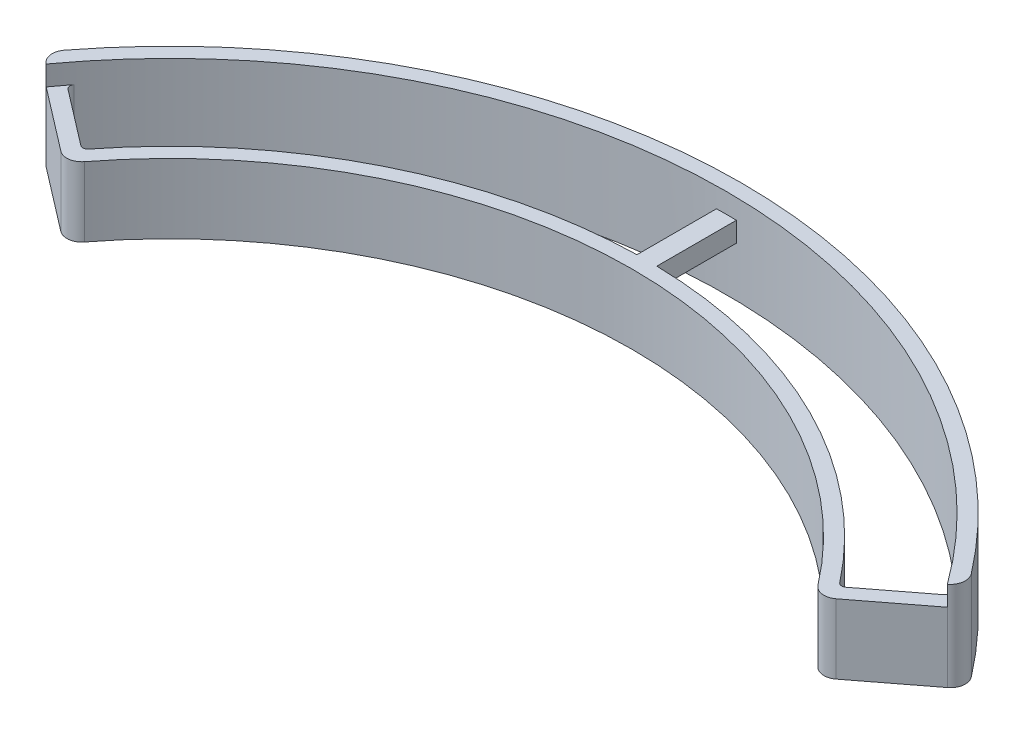
SolidWorks part; units mm, degrees
ref_plane "Front Plane" through (0, 0, 0) normal (0, 0, 1) x (1, 0, 0)
ref_plane "Top Plane" through (0, 0, 0) normal (0, 1, 0) x (1, 0, 0)
ref_plane "Right Plane" through (0, 0, 0) normal (1, 0, 0) x (0, 0, -1)
sketch "Sketch1" plane through (0, 0, 0) normal (0, 1, 0) x (1, 0, 0)
  line L0 (37.7849, 27.1026) -> (46.5154, 33.8018)
  line L1 (-37.7849, 27.1026) -> (-46.5154, 33.8018)
  line L2 (0, 48) -> (0, 56) construction
  line L3 (-38.081, 29.2205) -> (0, 0) construction
  line L4 (38.081, 29.2205) -> (0, 0) construction
  line L5 (-38.081, 29.2205) -> (-44.4278, 34.0906)
  line L6 (38.081, 29.2205) -> (44.4278, 34.0906)
  arc A0 (-44.4278, 34.0906) -> (44.4278, 34.0906) centre (0, 0) cw
  arc A1 (-38.081, 29.2205) -> (38.081, 29.2205) centre (0, 0) cw
  arc A2 (-37.7849, 27.1026) -> (37.7849, 27.1026) centre (0, 0) cw
  arc A3 (-46.5154, 33.8018) -> (46.5154, 33.8018) centre (0, 0) cw
  dimension "D1" = 56
  dimension "D2" = 105
  dimension "D3" = 8
  dimension "D4" = 1.5
extrude "Boss-Extrude1" add sketch "Sketch1" against normal blind 7
sketch "Sketch2" plane through (0, 0, 0) normal (0, 1, 0) x (1, 0, 0)
  line L1 (-1, 56.7595) -> (1, 56.7595)
  line L2 (-1, 56.7595) -> (-1, 47.003)
  line L3 (-1, 47.003) -> (1, 47.003)
  line L4 (1, 56.7595) -> (1, 47.003)
  line L5 (-1, 56.7595) -> (1, 47.003) construction
  line L6 (-1, 47.003) -> (1, 56.7595) construction
  point P0 (0, 51.8812)
  dimension "D1" = 2
extrude "Boss-Extrude2" add sketch "Sketch2" against normal blind 2
sketch "Sketch3" plane through (0, 0, 0) normal (0, 1, 0) x (1, 0, 0)
  line L0 (-46.5154, 33.8018) -> (-37.7849, 27.1026) construction
  line L1 (37.7849, 27.1026) -> (46.5154, 33.8018) construction
  line L2 (45.325, 32.8884) -> (46.5154, 33.8018)
  line L3 (-45.325, 32.8884) -> (-46.5154, 33.8018)
  arc A1 (-46.5154, 33.8018) -> (46.5154, 33.8018) centre (0, 0) cw
  arc A2 (-45.325, 32.8884) -> (45.325, 32.8884) centre (0, 0) cw
  arc A3 (44.4278, 34.0906) -> (1, 55.9911) centre (0, 0) ccw construction
extrude "Boss-Extrude3" add sketch "Sketch3" along normal blind 2
fillet "Fillet1" radius 0.5 4 edges at (-38.081, -3.5, -29.2205) (38.081, -3.5, -29.2205)
fillet "Fillet2" radius 1.5 4 edges at (46.5154, -2.5, -33.8018) (37.7849, -3.5, -27.1026) (-37.7849, -3.5, -27.1026) (-46.5154, -2.5, -33.8018)
